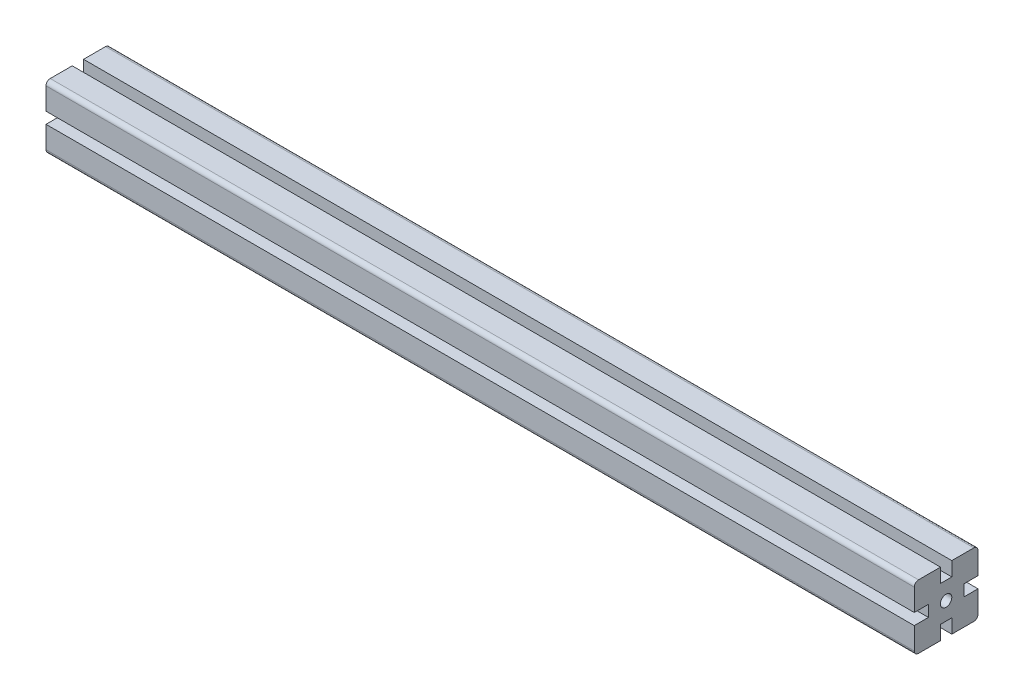
SolidWorks part; units mm, degrees
ref_plane "Plan de face" through (0, 0, 0) normal (0, 0, 1) x (1, 0, 0)
ref_plane "Plan de dessus" through (0, 0, 0) normal (0, 1, 0) x (1, 0, 0)
ref_plane "Plan de droite" through (0, 0, 0) normal (1, 0, 0) x (0, 0, -1)
ref_plane "Plan1" through (1000, 0, 0) normal (1, 0, 0) x (0, 0, -1)
sketch "Esquisse1" plane through (1000, 0, 0) normal (1, 0, 0) x (0, 0, -1)
  line L0 (22.5, -4) -> (12.5, -4)
  line L1 (12.5, -4) -> (12.5, 4)
  line L2 (12.5, 4) -> (22.5, 4)
  line L3 (22.5, 4) -> (22.5, 22.5)
  line L4 (22.5, 22.5) -> (4, 22.5)
  line L5 (4, 22.5) -> (4, 12.5)
  line L6 (4, 12.5) -> (-4, 12.5)
  line L7 (-4, 12.5) -> (-4, 22.5)
  line L8 (-4, 22.5) -> (-22.5, 22.5)
  line L9 (-22.5, 22.5) -> (-22.5, 4)
  line L10 (-22.5, 4) -> (-12.5, 4)
  line L11 (-12.5, 4) -> (-12.5, -4)
  line L12 (-12.5, -4) -> (-22.5, -4)
  line L13 (-22.5, -4) -> (-22.5, -22.5)
  line L14 (-22.5, -22.5) -> (-4, -22.5)
  line L15 (-4, -22.5) -> (-4, -12.5)
  line L16 (-4, -12.5) -> (4, -12.5)
  line L17 (4, -12.5) -> (4, -22.5)
  line L18 (4, -22.5) -> (22.5, -22.5)
  line L19 (22.5, -22.5) -> (22.5, -4)
  line L20 (0, 0) -> (22.5, 0) construction
  line L21 (0, 0) -> (0, 22.5) construction
  circle A0 centre (0, 0) radius 4
  dimension "D5" = 10
  dimension "D9" = 22.5
  dimension "D10" = 8
  dimension "D1" = 4
  dimension "D2" = 45
  dimension "D3" = 45
  dimension "D4" = 4
  dimension "D6" = 10
  dimension "D7" = 10
  dimension "D8" = 10
extrude "Boss.-Extru.1" add sketch "Esquisse1" against normal blind 613
fillet "Congé1" radius 3 4 edges at (693.5, -22.5, -22.5) (693.5, -22.5, 22.5) (693.5, 22.5, 22.5) (693.5, 22.5, -22.5)
